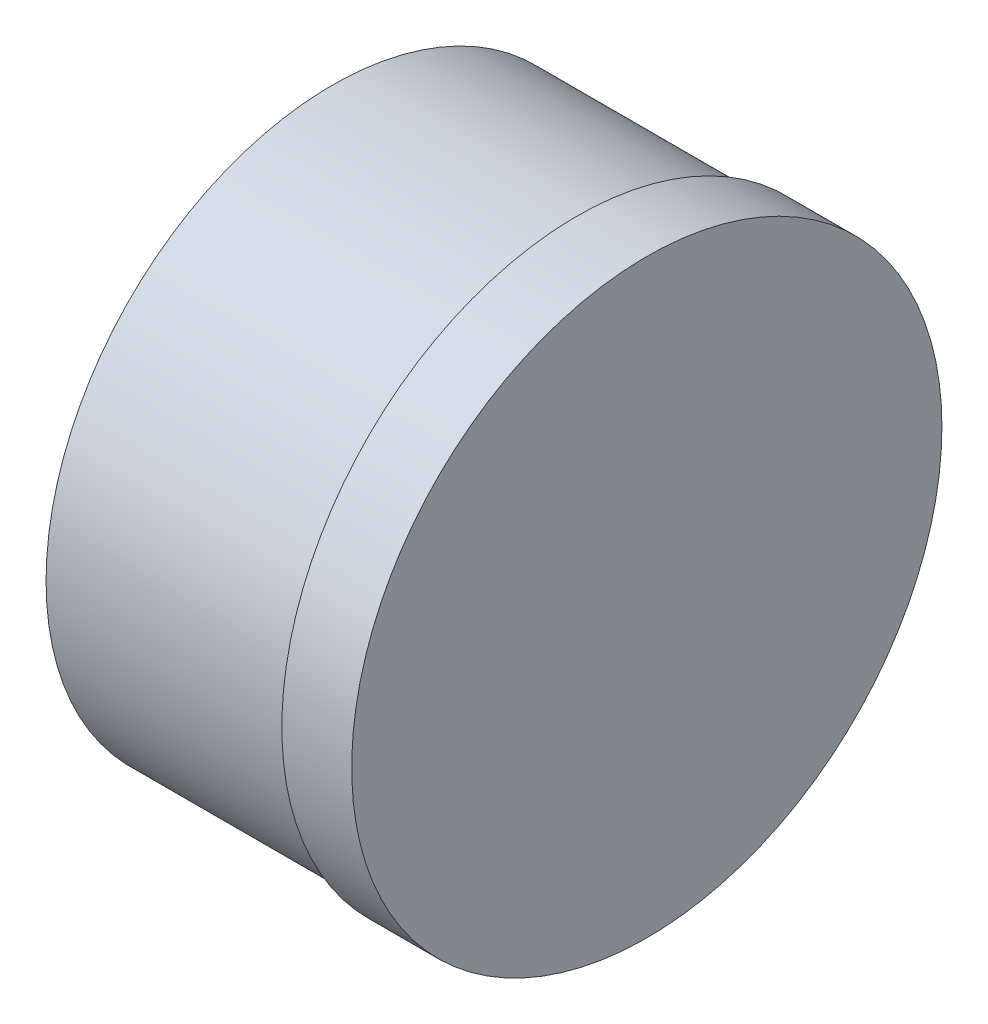
SolidWorks part; units mm, degrees
ref_plane "Front Plane" through (0, 0, 0) normal (0, 0, 1) x (1, 0, 0)
ref_plane "Top Plane" through (0, 0, 0) normal (0, 1, 0) x (1, 0, 0)
ref_plane "Right Plane" through (0, 0, 0) normal (1, 0, 0) x (0, 0, -1)
sketch "Sketch1" plane through (0, 0, 0) normal (1, 0, 0) x (0, 0, -1)
  circle A0 centre (0, 0) radius 41
  dimension "D1" = 82
extrude "Boss-Extrude1" add sketch "Sketch1" along normal blind 35
sketch "Sketch2" plane through (35, 0, 0) normal (1, 0, 0) x (0, 0, -1)
  circle A0 centre (0, 0) radius 42.25
  dimension "D1" = 84.5
extrude "Boss-Extrude2" add sketch "Sketch2" along normal blind 10
ref_plane "Bolts" through (0, 41, 0) normal (0, 1, 0) x (1, 0, 0)
